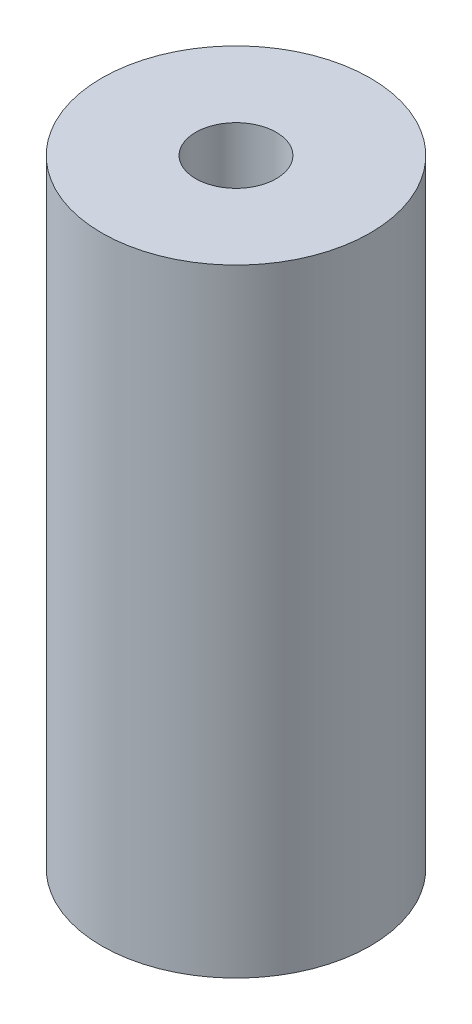
SolidWorks part; units mm, degrees
ref_plane "Alzado" through (0, 0, 0) normal (0, 0, 1) x (1, 0, 0)
ref_plane "Planta" through (0, 0, 0) normal (0, 1, 0) x (1, 0, 0)
ref_plane "Vista lateral" through (0, 0, 0) normal (1, 0, 0) x (0, 0, -1)
sketch "Croquis1" plane through (0, 0, 0) normal (0, 1, 0) x (1, 0, 0)
  circle A0 centre (0, 0) radius 5
  dimension "D1" = 10
extrude "Saliente-Extruir1" add sketch "Croquis1" along normal blind 23
sketch "Croquis2" plane through (0, 23, 0) normal (0, 1, 0) x (1, 0, 0)
  circle A0 centre (0, 0) radius 1.5
  dimension "D1" = 3
extrude "Cortar-Extruir1" cut sketch "Croquis2" against normal blind 5
sketch "Croquis4" plane through (0, 0, 0) normal (0, -1, 0) x (1, 0, 0)
  circle A0 centre (0, 0) radius 1.5
  dimension "D1" = 3
extrude "Cortar-Extruir2" cut sketch "Croquis4" against normal blind 5
